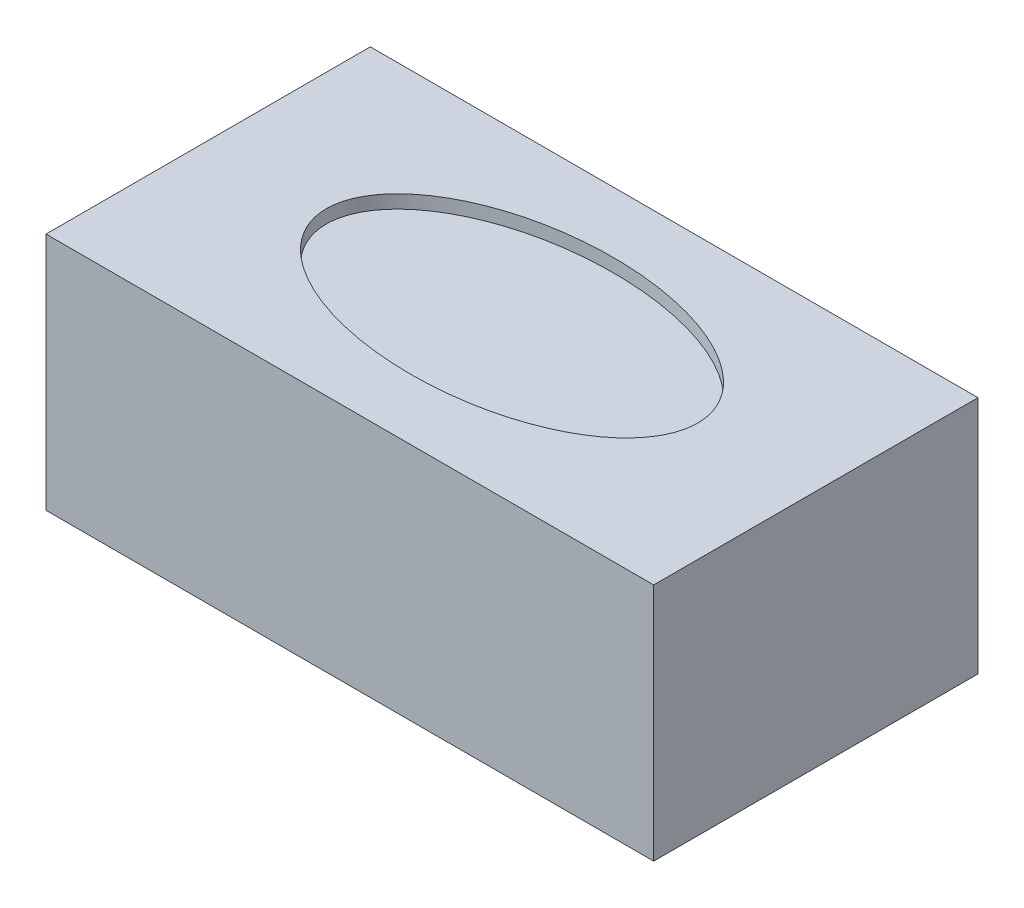
SolidWorks part; units mm, degrees
ref_plane "Front Plane" through (0, 0, 0) normal (0, 0, 1) x (1, 0, 0)
ref_plane "Top Plane" through (0, 0, 0) normal (0, 1, 0) x (1, 0, 0)
ref_plane "Right Plane" through (0, 0, 0) normal (1, 0, 0) x (0, 0, -1)
sketch "Sketch1" plane through (0, 0, 0) normal (0, 1, 0) x (1, 0, 0)
  line L1 (-114.3, -61) -> (114.3, -61)
  line L2 (-114.3, -61) -> (-114.3, 61)
  line L3 (-114.3, 61) -> (114.3, 61)
  line L4 (114.3, -61) -> (114.3, 61)
  line L5 (-114.3, -61) -> (114.3, 61) construction
  line L6 (-114.3, 61) -> (114.3, -61) construction
  point P0 (0, 0)
  dimension "D1" = 122
  dimension "D2" = 228.6
extrude "Boss-Extrude1" add sketch "Sketch1" along normal blind 90
sketch "Sketch2" plane through (0, 90, 0) normal (0, 1, 0) x (1, 0, 0)
  line L0 (0, -38.1) -> (0, 38.1) construction
  line L1 (-69.85, 0) -> (0, 0) construction
  line L2 (0, 0) -> (69.85, 0) construction
  ellipse E0 centre (0, 0) end of major axis (-69.85, 0) minor radius 38.1
  dimension "D1" = 139.7
  dimension "D2" = 76.2
extrude "Cut-Extrude1" cut sketch "Sketch2" against normal blind 5
